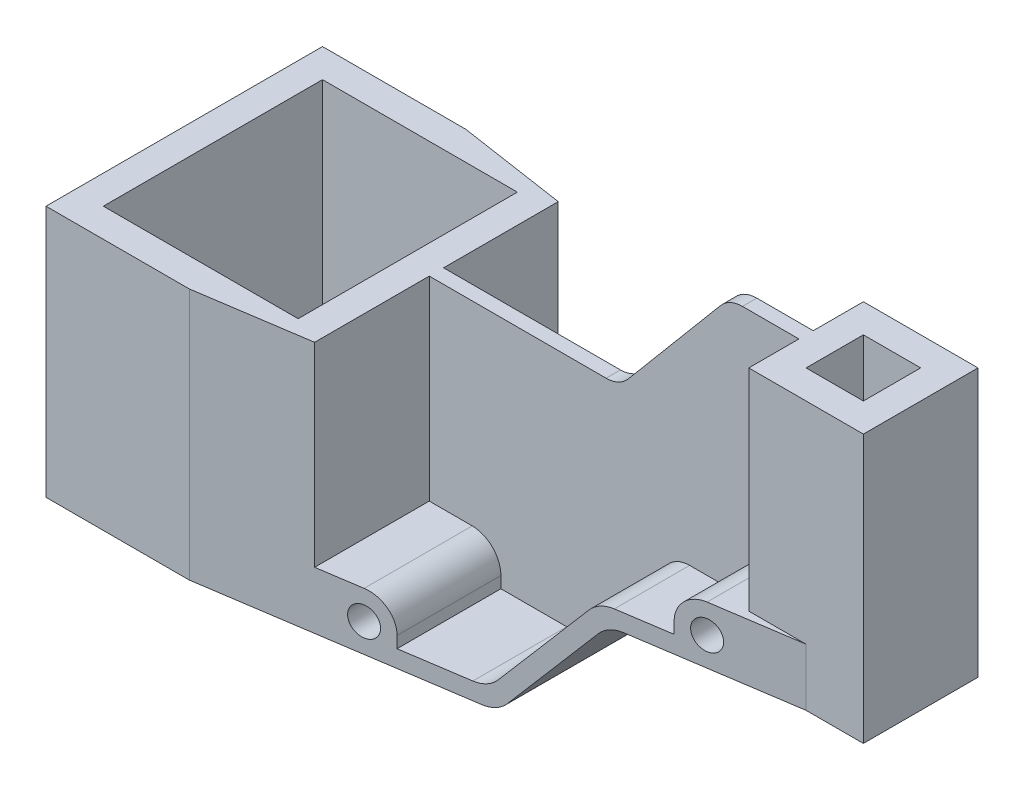
SolidWorks part; units mm, degrees
material "1060 Alloy"
ref_plane "Front Plane" through (0, 0, 0) normal (0, 0, 1) x (1, 0, 0)
ref_plane "Top Plane" through (0, 0, 0) normal (0, 1, 0) x (1, 0, 0)
ref_plane "Right Plane" through (0, 0, 0) normal (1, 0, 0) x (0, 0, -1)
sketch "Sketch1" plane through (0, 0, 0) normal (0, 0, 1) x (1, 0, 0)
  line L1 (-34.5107, 107.7078) -> (222.4893, 107.7078)
  line L2 (-34.5107, 107.7078) -> (-34.5107, -25.7922)
  line L3 (-34.5107, -25.7922) -> (222.4893, -25.7922)
  line L4 (222.4893, 107.7078) -> (222.4893, -25.7922)
extrude "Boss-Extrude1" add sketch "Sketch1" along normal blind 96.5
sketch "Sketch2" plane through (0, 0, 96.5) normal (0, 0, 1) x (1, 0, 0)
  line L5 (-34.5107, 107.7078) -> (78.4893, 107.7078)
  line L6 (-34.5107, 107.7078) -> (-34.5107, 62.2078)
  line L7 (-34.5107, 62.2078) -> (78.4893, 62.2078)
  line L8 (78.4893, 107.7078) -> (78.4893, 62.2078)
  line L9 (222.4893, -25.7922) -> (142.4893, -25.7922)
  line L10 (222.4893, -25.7922) -> (222.4893, 14.2078)
  line L11 (222.4893, 14.2078) -> (142.4893, 14.2078)
  line L12 (142.4893, -25.7922) -> (142.4893, 14.2078)
extrude "Cut-Extrude1" cut sketch "Sketch2" against normal blind 96.5
sketch "Sketch4" plane through (0, 62.2078, 0) normal (0, 1, 0) x (1, 0, 0)
  line L5 (-34.5107, -96.5) -> (78.4893, -96.5) construction
  line L6 (-34.5107, 0) -> (53.4893, 0)
  line L7 (-34.5107, 0) -> (-34.5107, -48.25)
  line L9 (53.4893, 0) -> (53.4893, -48.25)
  line L11 (-34.5107, -48.25) -> (-34.5107, -96.5)
  line L12 (-34.5107, -96.5) -> (53.4893, -96.5)
  line L13 (53.4893, -48.25) -> (53.4893, -96.5)
  line L14 (-24.5107, -10) -> (-24.5107, -48.25)
  line L15 (-24.5107, -48.25) -> (-24.5107, -86.5)
  line L16 (-24.5107, -86.5) -> (43.4893, -86.5)
  line L17 (43.4893, -48.25) -> (43.4893, -86.5)
  line L18 (43.4893, -10) -> (43.4893, -48.25)
  line L19 (-24.5107, -10) -> (43.4893, -10)
  point P16 (9.4893, -96.5)
  dimension "D1" = 48.25
  dimension "D2" = 48.25
  dimension "D3" = 88
  dimension "D5" = 10
  dimension "D6" = 10
  dimension "D7" = 44
  dimension "D4" = 10
extrude "Cut-Extrude2" cut sketch "Sketch4" against normal blind 88 contours L14 L15 L16 L17 L18 L19
sketch "Sketch6" plane through (0, 107.7078, 0) normal (0, 1, 0) x (1, 0, 0)
  line L1 (222.4893, -96.5) -> (222.4893, 0) construction
  line L2 (222.4893, -28.25) -> (222.4893, 0)
  line L3 (222.4893, 0) -> (78.4893, 0) construction
  line L4 (222.4893, 0) -> (202.4893, 0)
  line L5 (202.4893, 0) -> (202.4893, -28.25)
  line L6 (202.4893, -28.25) -> (222.4893, -28.25)
  line L7 (222.4893, -96.5) -> (222.4893, -68.25)
  line L8 (222.4893, -68.25) -> (202.4893, -68.25)
  line L9 (202.4893, -68.25) -> (202.4893, -96.5)
  line L10 (222.4893, -96.5) -> (78.4893, -96.5) construction
  line L11 (202.4893, -96.5) -> (222.4893, -96.5)
extrude "Cut-Extrude3" cut sketch "Sketch6" against normal blind 93.5
sketch "Sketch7" plane through (0, 107.7078, 0) normal (0, 1, 0) x (1, 0, 0)
  line L0 (202.4893, -28.25) -> (202.4893, 0)
  line L1 (202.4893, 0) -> (78.4893, 0)
  line L2 (78.4893, 0) -> (78.4893, -28.25)
  line L3 (78.4893, 0) -> (78.4893, -96.5) construction
  line L4 (78.4893, -28.25) -> (202.4893, -28.25)
  line L5 (202.4893, -68.25) -> (78.4893, -68.25)
  line L6 (78.4893, -68.25) -> (78.4893, -96.5)
  line L7 (78.4893, -96.5) -> (202.4893, -96.5)
  line L8 (202.4893, -96.5) -> (202.4893, -68.25)
extrude "Cut-Extrude4" cut sketch "Sketch7" against normal blind 73.5
sketch "Sketch8" plane through (0, 107.7078, 0) normal (0, 1, 0) x (1, 0, 0)
  line L1 (78.4893, -28.25) -> (222.4893, -28.25) construction
  line L5 (78.4893, -28.25) -> (78.4893, -68.25) construction
  line L13 (182.4893, -28.25) -> (78.4893, -28.25)
  line L14 (182.4893, -28.25) -> (182.4893, -45.75)
  line L15 (182.4893, -45.75) -> (78.4893, -45.75)
  line L16 (78.4893, -28.25) -> (78.4893, -45.75)
  line L17 (222.4893, -68.25) -> (78.4893, -68.25) construction
  line L18 (182.4893, -68.25) -> (78.4893, -68.25)
  line L19 (182.4893, -68.25) -> (182.4893, -50.75)
  line L20 (182.4893, -50.75) -> (78.4893, -50.75)
  line L21 (78.4893, -68.25) -> (78.4893, -50.75)
extrude "Cut-Extrude5" cut sketch "Sketch8" against normal blind 73.5
sketch "Sketch9" plane through (0, 62.2078, 0) normal (0, 1, 0) x (1, 0, 0)
  line L0 (-34.5107, -96.5) -> (78.4893, -96.5) construction
  line L1 (78.4893, -50.75) -> (53.4893, -50.75)
  line L2 (78.4893, -50.75) -> (78.4893, -96.5)
  line L3 (78.4893, -96.5) -> (53.4893, -96.5)
  line L4 (53.4893, -50.75) -> (53.4893, -96.5)
  line L5 (-34.5107, 0) -> (78.4893, 0) construction
  line L6 (78.4893, -45.75) -> (53.4893, -45.75)
  line L7 (78.4893, -45.75) -> (78.4893, 0)
  line L8 (78.4893, 0) -> (53.4893, 0)
  line L9 (53.4893, -45.75) -> (53.4893, 0)
extrude "Cut-Extrude6" cut sketch "Sketch9" against normal blind 68
sketch "Sketch11" plane through (0, 34.2078, 0) normal (0, 1, 0) x (1, 0, 0)
  line L0 (78.4893, -96.5) -> (202.4893, -96.5) construction
  line L6 (78.4893, -50.75) -> (162.4893, -50.75)
  line L7 (78.4893, -50.75) -> (78.4893, -96.5)
  line L8 (78.4893, -96.5) -> (162.4893, -96.5)
  line L9 (162.4893, -50.75) -> (162.4893, -96.5)
extrude "Cut-Extrude7" cut sketch "Sketch11" against normal blind 14 contours L7 L6 L9 L8
sketch "Sketch12" plane through (0, 34.2078, 0) normal (0, 1, 0) x (1, 0, 0)
  line L0 (202.4893, 0) -> (78.4893, 0) construction
  line L6 (78.4893, 0) -> (162.4893, 0)
  line L7 (78.4893, 0) -> (78.4893, -45.75)
  line L8 (78.4893, -45.75) -> (162.4893, -45.75)
  line L9 (162.4893, 0) -> (162.4893, -45.75)
extrude "Cut-Extrude8" cut sketch "Sketch12" against normal blind 14 contours L7 L6 L9 L8
sketch "Sketch13" plane through (0, 0, 96.5) normal (0, 0, 1) x (1, 0, 0)
  line L0 (142.4893, 14.2078) -> (108.9253, -25.7922)
  line L3 (139.6915, 20.2078) -> (106.1275, -19.7922)
  line L4 (-34.5107, -25.7922) -> (142.4893, -25.7922) construction
  line L5 (139.6915, 20.2078) -> (78.4893, 20.2078)
  line L6 (78.4893, 20.2078) -> (162.4893, 20.2078) construction
  line L7 (78.4893, 20.2078) -> (78.4893, -19.7922)
  line L8 (78.4893, -19.7922) -> (106.1275, -19.7922)
  dimension "D1" = 6
  dimension "D2" = 130
  dimension "D3" = 6
extrude "Cut-Extrude10" cut sketch "Sketch13" against normal blind 45.75 contours L8 L3 L5 L7
sketch "Sketch15" plane through (0, 0, 96.5) normal (0, 0, 1) x (1, 0, 0)
  line L0 (142.4893, 14.2078) -> (108.9253, -25.7922)
  line L1 (-34.5107, -25.7922) -> (142.4893, -25.7922) construction
  line L2 (139.6915, 20.2078) -> (106.1275, -19.7922) construction
  line L3 (142.4893, 14.2078) -> (142.4893, -25.7922)
  line L4 (142.4893, -25.7922) -> (108.9253, -25.7922)
  dimension "D1" = 6
extrude "Cut-Extrude11" cut sketch "Sketch15" against normal blind 96.5 contours L4 L0 L3
sketch "Sketch16" plane through (0, 0, 0) normal (0, 0, -1) x (-1, 0, 0)
  line L0 (-78.4893, -5.7922) -> (-78.4893, -19.7922)
  line L1 (-78.4893, -19.7922) -> (-106.1275, -19.7922)
  line L2 (-106.1275, -19.7922) -> (-139.6915, 20.2078)
  line L3 (-78.4893, 20.2078) -> (-162.4893, 20.2078) construction
  line L4 (-139.6915, 20.2078) -> (-78.4893, 20.2078)
  line L5 (-78.4893, 20.2078) -> (-78.4893, -19.7922)
  line L6 (34.5107, -25.7922) -> (-108.9253, -25.7922) construction
  line L8 (-142.4893, 14.2078) -> (-108.9253, -25.7922)
  dimension "D1" = 6
  dimension "D2" = 6
  dimension "D3" = 130
extrude "Cut-Extrude12" cut sketch "Sketch16" against normal blind 45.75 contours L1 L2 L4 L5
sketch "Sketch17" plane through (0, 0, 50.75) normal (0, 0, 1) x (1, 0, 0)
  line L6 (78.4893, 62.2078) -> (119.8621, 62.2078)
  line L7 (119.8621, 62.2078) -> (158.1482, 107.7078)
  line L8 (182.4893, 107.7078) -> (78.4893, 107.7078) construction
  line L9 (158.1482, 107.7078) -> (78.4893, 107.7078)
  line L10 (78.4893, 107.7078) -> (78.4893, 62.2078)
  line L11 (139.6915, 20.2078) -> (106.1275, -19.7922) construction
  point P2 (122.9095, 0.2078)
  dimension "D1" = 42.25
extrude "Cut-Extrude13" cut sketch "Sketch17" against normal blind 5
sketch "Sketch18" plane through (0, 0, 96.5) normal (0, 0, 1) x (1, 0, 0)
  circle A0 centre (172.4893, 24.2078) radius 5
  circle A1 centre (68.4893, -15.7922) radius 5
extrude "Cut-Extrude14" cut sketch "Sketch18" against normal blind 96.5
sketch "Sketch19" plane through (0, 107.7078, 0) normal (0, 1, 0) x (1, 0, 0)
  line L0 (212.4893, -38.25) -> (212.4893, -58.25)
  line L5 (212.4893, -58.25) -> (192.4893, -58.25)
  line L6 (192.4893, -38.25) -> (192.4893, -58.25)
  line L7 (212.4893, -38.25) -> (192.4893, -38.25)
extrude "Cut-Extrude15" cut sketch "Sketch19" against normal blind 93.5 contours L0 L5 L6 L7
sketch "Sketch51" plane through (0, 62.2078, 0) normal (0, 1, 0) x (1, 0, 0)
  line L0 (9.4893, -96.5) -> (15.4893, -96.5)
  line L1 (-34.5107, -96.5) -> (53.4893, -96.5) construction
  line L4 (15.4893, -96.5) -> (53.4893, -96.5)
  line L5 (53.4893, -96.5) -> (53.4893, -90.7594)
  line L6 (53.4893, -90.7594) -> (15.4893, -96.5)
extrude "Cut-Extrude42" cut sketch "Sketch51" against normal blind 88 contours L4 L5 L6
sketch "Sketch62" plane through (0, 14.2078, 0) normal (0, -1, 0) x (1, 0, 0)
  line L2 (142.4893, 96.5) -> (202.4893, 96.5)
  line L3 (202.4893, 96.5) -> (202.4893, 68.25)
  line L4 (142.4893, 96.5) -> (142.4893, 77.3142)
  line L5 (142.4893, 0) -> (142.4893, 96.5) construction
  line L6 (142.4893, 77.3142) -> (202.4893, 68.25)
extrude "Cut-Extrude53" cut sketch "Sketch62" against normal blind 20
sketch "Sketch75" plane through (0, -25.7922, 0) normal (0, -1, 0) x (1, 0, 0)
  line L0 (142.4893, 77.3142) -> (53.4893, 90.7594)
  line L2 (53.4893, 90.7594) -> (53.4893, 96.5)
  line L3 (53.4893, 96.5) -> (142.4893, 96.5)
  line L4 (142.4893, 96.5) -> (142.4893, 77.3142)
extrude "Cut-Extrude61" cut sketch "Sketch75" against normal blind 50.68
sketch "Sketch79" plane through (0, 62.2078, 0) normal (0, 1, 0) x (1, 0, 0)
  line L1 (-34.5107, 0) -> (53.4893, 0) construction
  line L3 (15.4893, 0) -> (53.4893, 0)
  line L4 (53.4893, 0) -> (53.4893, -5.7406)
  line L5 (53.4893, 0) -> (53.4893, -45.75) construction
  line L6 (53.4893, -5.7406) -> (15.4893, 0)
extrude "Cut-Extrude62" cut sketch "Sketch79" against normal blind 88
sketch "Sketch80" plane through (0, -25.7922, 0) normal (0, -1, 0) x (1, 0, 0)
  line L1 (53.4893, 5.7406) -> (53.4893, 0)
  line L2 (53.4893, 0) -> (142.4893, 0)
  line L3 (142.4893, 0) -> (142.4893, 19.1858)
  line L4 (142.4893, 19.1858) -> (53.4893, 5.7406)
extrude "Cut-Extrude63" cut sketch "Sketch80" against normal blind 88
sketch "Sketch81" plane through (0, 14.2078, 0) normal (0, -1, 0) x (1, 0, 0)
  line L0 (142.4893, 19.1858) -> (202.4893, 28.25)
  line L1 (202.4893, 28.25) -> (202.4893, 0)
  line L2 (202.4893, 0) -> (142.4893, 0)
  line L3 (142.4893, 0) -> (142.4893, 19.1858)
extrude "Cut-Extrude64" cut sketch "Sketch81" against normal blind 88
fillet "Fillet2" radius 10 1 edges at (162.4893, 34.2078, 62.5214)
fillet "Fillet3" radius 10 1 edges at (162.4893, 34.2078, 33.9786)
fillet "Fillet4" radius 10 1 edges at (139.6915, 20.2078, 32.2566)
fillet "Fillet5" radius 10 1 edges at (139.6915, 20.2078, 64.2434)
fillet "Fillet6" radius 10 1 edges at (106.1275, -19.7922, 66.7787)
fillet "Fillet7" radius 10 1 edges at (106.1275, -19.7922, 29.7213)
fillet "Fillet8" radius 10 1 edges at (78.4893, -5.7922, 68.8663)
fillet "Fillet9" radius 10 1 edges at (78.4893, -5.7922, 27.6337)
fillet "Fillet10" radius 10 1 edges at (158.1482, 107.7078, 48.25)
fillet "Fillet11" radius 10 1 edges at (119.8621, 62.2078, 48.25)
fillet "Fillet12" radius 10 1 edges at (142.4893, 14.2078, 48.25)
fillet "Fillet13" radius 10 1 edges at (108.9253, -25.7922, 48.25)
sketch "Sketch82" plane through (0, 0, 0) normal (0, 1, 0) x (1, 0, 0)
  line L1 (-64.0809, -48.25) -> (252.4111, -48.25) construction
  line L2 (202.4893, -133.1754) -> (202.4893, 45.8185)
  line L3 (9.4893, 45.8185) -> (9.4893, -133.1754) construction
  line L4 (53.4893, -5.7406) -> (53.4893, -45.75) construction
  line L5 (-34.5107, 0) -> (-34.5107, -96.5) construction
  line L7 (-34.5107, 0) -> (15.4893, 0) construction
  line L8 (222.4893, -68.25) -> (222.4893, -28.25) construction
  line L9 (182.4893, -45.75) -> (182.4893, -28.25) construction
  line L10 (78.4893, -45.75) -> (101.4644, -45.75) construction
  line L11 (78.4893, -50.75) -> (101.4644, -50.75) construction
  line L12 (-24.5107, -10) -> (-24.5107, -86.5) construction
  line L13 (53.4893, -50.75) -> (53.4893, -90.7594) construction
  line L14 (43.4893, -10) -> (43.4893, -86.5) construction
  line L15 (-24.5107, -10) -> (43.4893, -10) construction
  point P19 (89.9769, -45.75)
  point P22 (89.9769, -50.75)
  dimension "D1" = 193
  dimension "D2" = 88
  dimension "D3" = 48.25
  dimension "D4" = 20
  dimension "D5" = 40
  dimension "D6" = 6
  dimension "D7" = 5
  dimension "D8" = 2.5
  dimension "D9" = 10
  dimension "D10" = 10
  dimension "D11" = 10
  dimension "D12" = 44
sketch "Sketch83" plane through (0, 0, 0) normal (0, 0, 1) x (1, 0, 0)
  line L1 (-34.5107, -25.7922) -> (-34.5107, 62.2078)
  line L2 (-34.5107, 62.2078) -> (53.4893, 62.2078)
  line L3 (53.4893, 62.2078) -> (53.4893, -5.7922)
  line L4 (53.4893, -5.7922) -> (53.4893, 62.2078) construction
  line L5 (53.4893, -5.7922) -> (53.4893, 62.2078) construction
  line L8 (104.2622, -25.7922) -> (15.4893, -25.7922) construction
  line L9 (78.4893, -25.7922) -> (-34.5107, -25.7922)
  line L11 (172.4893, 34.2078) -> (202.4893, 34.2078) construction
  line L12 (147.1524, 14.2078) -> (202.4893, 14.2078) construction
  line L13 (182.4893, 34.2078) -> (182.4893, 107.7078) construction
  line L14 (222.4893, 14.2078) -> (222.4893, 107.7078) construction
  line L15 (136.6941, 16.6357) -> (109.1248, -16.2201) construction
  line L16 (139.4919, 10.6357) -> (111.9227, -22.2201) construction
  line L17 (78.4893, -19.7922) -> (101.4644, -19.7922) construction
  line L18 (136.6941, 16.6357) -> (109.1248, -16.2201) construction
  point P17 (267.6064, 149.4398)
  point P18 (289.2595, 132.5504)
  dimension "D1" = 88
  dimension "D2" = 103
  dimension "D3" = 88
  dimension "D4" = 10
  dimension "D5" = 20
  dimension "D6" = 40
  dimension "D7" = 10
  dimension "D8" = 6
  dimension "D9" = 6
  dimension "D10" = 130
  dimension "D11" = 50
  dimension "D12" = 20
